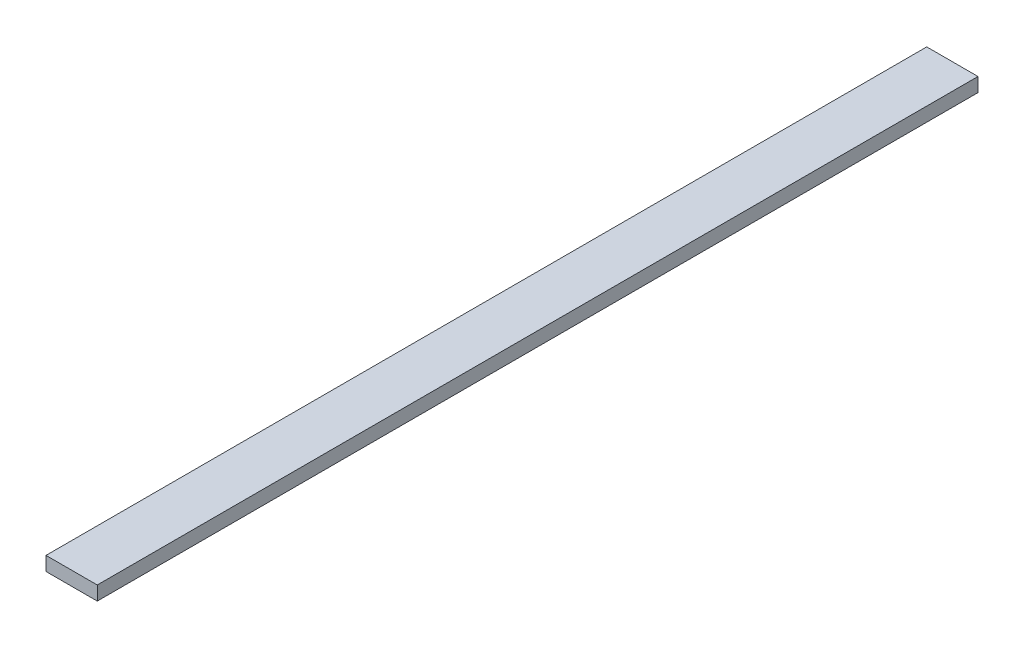
SolidWorks part; units mm, degrees
material "Maple"
ref_plane "Front Plane" through (0, 0, 0) normal (0, 0, 1) x (1, 0, 0)
ref_plane "Top Plane" through (0, 0, 0) normal (0, 1, 0) x (1, 0, 0)
ref_plane "Right Plane" through (0, 0, 0) normal (1, 0, 0) x (0, 0, -1)
sketch "Sketch1" plane through (0, 0, 0) normal (0, 0, 1) x (1, 0, 0)
  line L1 (0, 0) -> (139.7, 0)
  line L2 (0, 0) -> (0, 38.1)
  line L3 (0, 38.1) -> (139.7, 38.1)
  line L4 (139.7, 0) -> (139.7, 38.1)
  dimension "D1" = 38.1
  dimension "D2" = 139.7
extrude "Boss-Extrude1" add sketch "Sketch1" along normal blind 2438.4
sketch "Sketch2" plane through (0, 38.1, 0) normal (0, 1, 0) x (1, 0, 0)
  line L0 (0, -2438.4) -> (0, 0) construction
  line L1 (139.7, -2438.4) -> (0, -2438.4)
  line L2 (139.7, -2438.4) -> (139.7, -2400.3)
  line L3 (139.7, -2400.3) -> (0, -2400.3)
  line L4 (0, -2438.4) -> (0, -2400.3)
  dimension "D1" = 38.1
extrude "Cut-Extrude1" cut sketch "Sketch2" against normal through all
